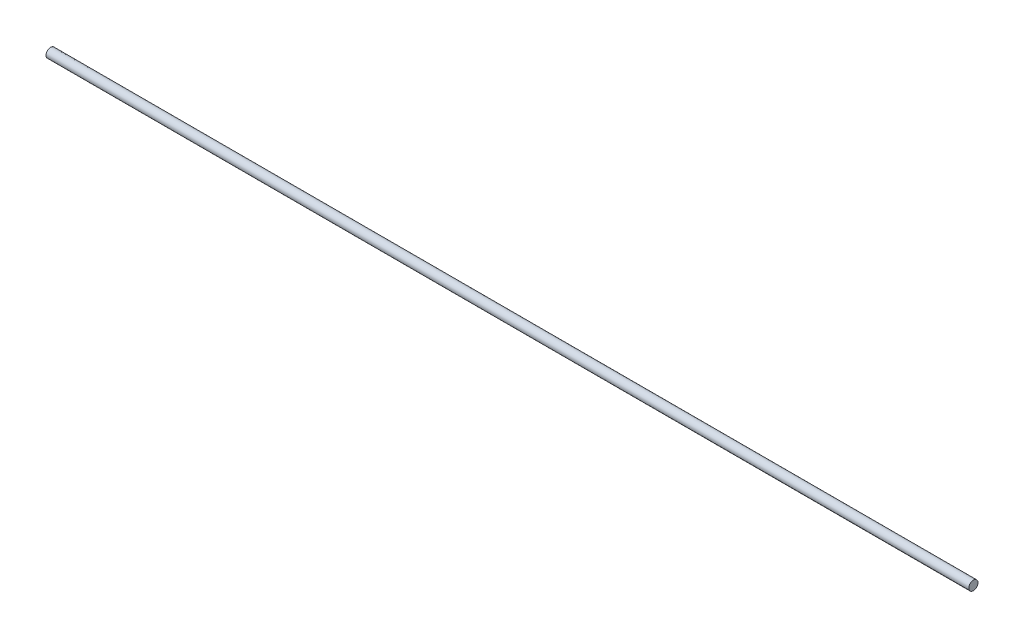
SolidWorks part; units mm, degrees
ref_plane "Front Plane" through (0, 0, 0) normal (0, 0, 1) x (1, 0, 0)
ref_plane "Top Plane" through (0, 0, 0) normal (0, 1, 0) x (1, 0, 0)
ref_plane "Right Plane" through (0, 0, 0) normal (1, 0, 0) x (0, 0, -1)
sketch "Sketch1" plane through (0, 0, 0) normal (1, 0, 0) x (0, 0, -1)
  circle A0 centre (0, 0) radius 4
  dimension "D1" = 8
extrude "Boss-Extrude1" add sketch "Sketch1" along normal blind 800 contours A0
